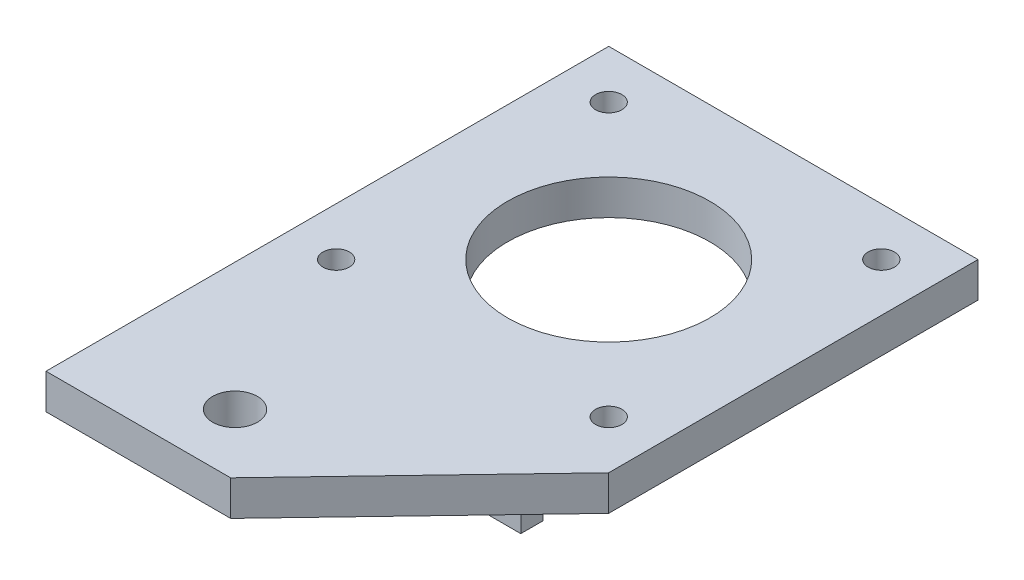
SolidWorks part; units mm, degrees
ref_plane "Front Plane" through (0, 0, 0) normal (0, 0, 1) x (1, 0, 0)
ref_plane "Top Plane" through (0, 0, 0) normal (0, 1, 0) x (1, 0, 0)
ref_plane "Right Plane" through (0, 0, 0) normal (1, 0, 0) x (0, 0, -1)
sketch "Sketch1" plane through (0, 0, 0) normal (0, 1, 0) x (1, 0, 0)
  line L0 (21, 42) -> (21, 0) construction
  line L1 (0, 0) -> (42, 0)
  line L2 (0, 0) -> (0, 42)
  line L3 (0, 42) -> (42, 42)
  line L4 (42, 0) -> (42, 42)
  line L5 (0, 21) -> (42, 21) construction
  line L6 (0, 0) -> (0, -22)
  line L7 (0, -22) -> (21, -22)
  line L8 (21, -22) -> (42, 0)
  line L9 (42, 0) -> (0, 0)
  circle A0 centre (5.5, 36.5) radius 1.5
  circle A1 centre (21, 21) radius 11.5
  circle A2 centre (36.5, 36.5) radius 1.5
  circle A3 centre (36.5, 5.5) radius 1.5
  circle A4 centre (5.5, 5.5) radius 1.5
  circle A5 centre (14.5, -15) radius 2.55
  point P23 (0, 0)
  dimension "D2" = 3
  dimension "D5" = 23
  dimension "D7" = 5.1
  dimension "D1" = 42
  dimension "D3" = 15.5
  dimension "D4" = 15.5
  dimension "D6" = 15
  dimension "D8" = 14.5
  dimension "D9" = 22
extrude "Boss-Extrude1" add sketch "Sketch1" along normal blind 4 contours L7 L8 L1 L6 A5 | L1 L4 L3 L2 A2 A1 A0 A3 A4
sketch "Sketch2" plane through (0, 0, 0) normal (0, -1, 0) x (1, 0, 0)
  line L0 (42, 0) -> (0, 0) construction
  line L1 (0, -42) -> (0, 22) construction
  line L2 (0, 3) -> (35, 3)
  line L3 (0, 3) -> (0, 0.5)
  line L4 (0, 0.5) -> (35, 0.5)
  line L5 (35, 3) -> (35, 0.5)
  point P10 (0, 0)
  dimension "D1" = 0.5
  dimension "D2" = 2.5
  dimension "D3" = 35
extrude "Boss-Extrude2" add sketch "Sketch2" along normal blind 4
equation "\"8mm hole\" = 8.4mm"
equation "\"22mm hole\"= 23mm"
equation "\"15mm hole\"= 15.8mm"
equation "\"bed height offset\"= 3mm"
equation "\"motor width\"= 42.5mm"
equation "\"D5@Sketch1\"= \"22mm hole\""
